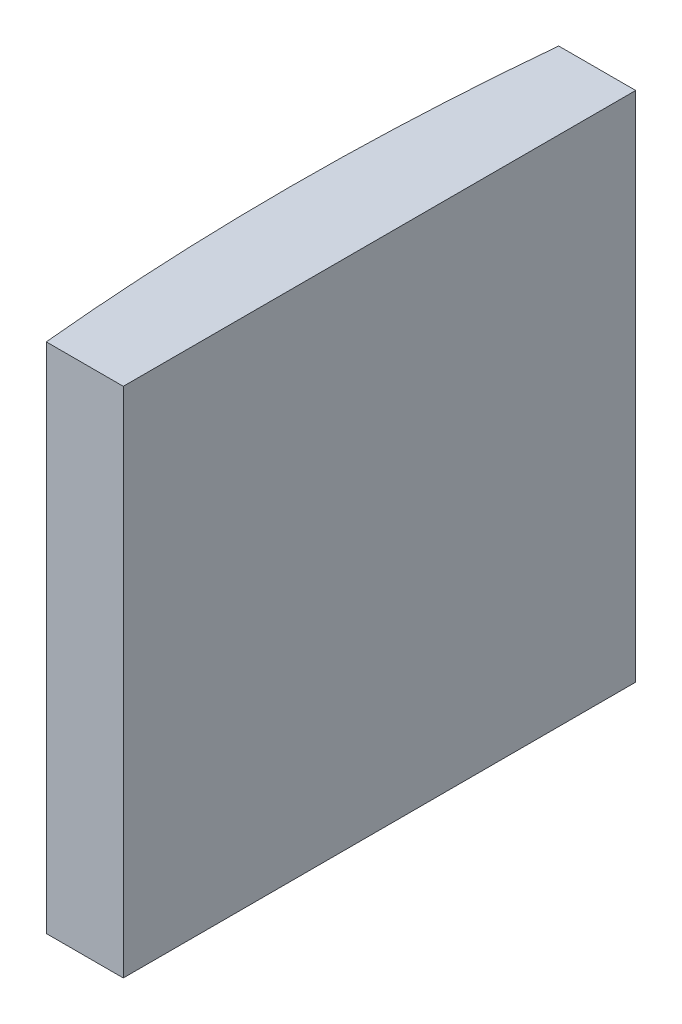
SolidWorks part; units mm, degrees
ref_plane "前视基准面" through (0, 0, 0) normal (0, 0, 1) x (1, 0, 0)
ref_plane "上视基准面" through (0, 0, 0) normal (0, 1, 0) x (1, 0, 0)
ref_plane "右视基准面" through (0, 0, 0) normal (1, 0, 0) x (0, 0, -1)
sketch "草图1" plane through (0, 0, 0) normal (0, 1, 0) x (1, 0, 0)
  line L0 (10.7432, 0) -> (-109.3032, 0) construction
  line L1 (-98.5601, 10) -> (-95.5548, 10)
  line L2 (-98.5601, -10) -> (-95.5548, -10)
  line L3 (-95.5548, 10) -> (-95.5548, -10)
  arc A0 (-98.5601, 10) -> (-98.5601, -10) centre (4.3552, 0) ccw
  point P2 (-109.3032, 0)
  point P19 (-99.0448, 0)
  point P20 (-95.5548, 0)
  dimension "D2" = 10
  dimension "D3" = 103.4
  dimension "D4" = 3.49
  dimension "D1" = 10
extrude "凸台-拉伸1" add sketch "草图1" along normal blind 20
